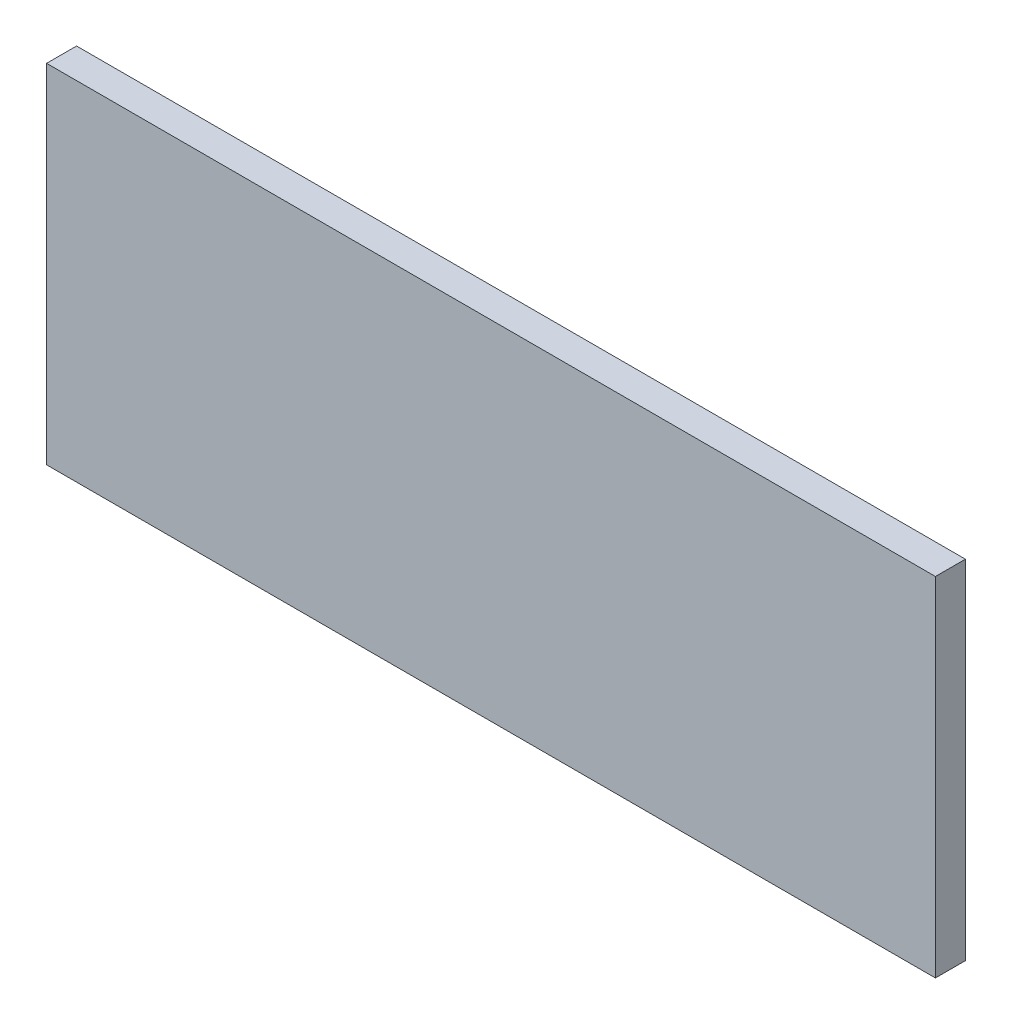
SolidWorks part; units mm, degrees
ref_plane "Plano frontal" through (0, 0, 0) normal (0, 0, 1) x (1, 0, 0)
ref_plane "Plano superior" through (0, 0, 0) normal (0, 1, 0) x (1, 0, 0)
ref_plane "Plano direito" through (0, 0, 0) normal (1, 0, 0) x (0, 0, -1)
sketch "Esboço1" plane through (0, 0, 0) normal (0, 0, 1) x (1, 0, 0)
  line L1 (-148.25, 58) -> (148.25, 58)
  line L2 (-148.25, 58) -> (-148.25, -58)
  line L3 (-148.25, -58) -> (148.25, -58)
  line L4 (148.25, 58) -> (148.25, -58)
  line L5 (-148.25, 58) -> (148.25, -58) construction
  line L6 (-148.25, -58) -> (148.25, 58) construction
  point P0 (0, 0)
  dimension "D1" = 116
  dimension "D2" = 296.5
extrude "Ressalto-extrusão1" add sketch "Esboço1" along normal mid plane 10
